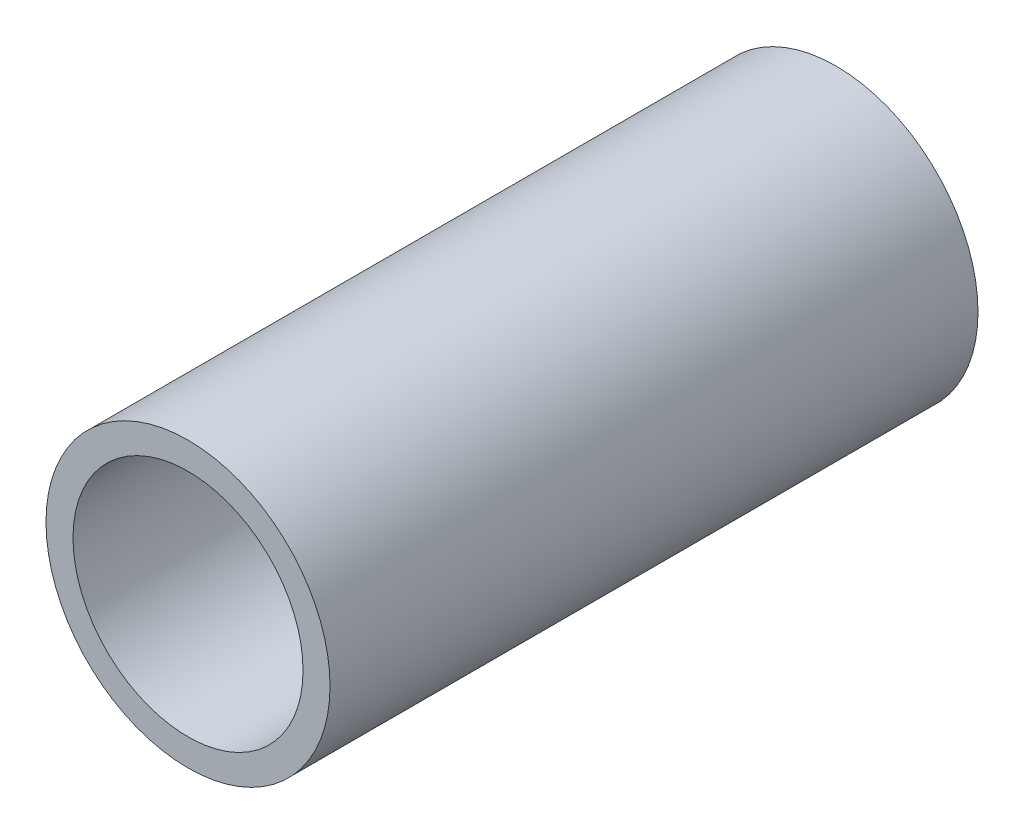
SolidWorks part; units mm, degrees
material "6061 Alloy"
ref_plane "Front Plane" through (0, 0, 0) normal (0, 0, 1) x (1, 0, 0)
ref_plane "Top Plane" through (0, 0, 0) normal (0, 1, 0) x (1, 0, 0)
ref_plane "Right Plane" through (0, 0, 0) normal (1, 0, 0) x (0, 0, -1)
sketch "Sketch1" plane through (0, 0, 0) normal (0, 0, 1) x (1, 0, 0)
  circle A0 centre (0, 0) radius 16.7005
  circle A1 centre (0, 0) radius 13.5255
  dimension "D1" = 33.401
  dimension "D2" = 3.175
extrude "Boss-Extrude1" add sketch "Sketch1" along normal blind 76.2 contours A1 | A0
